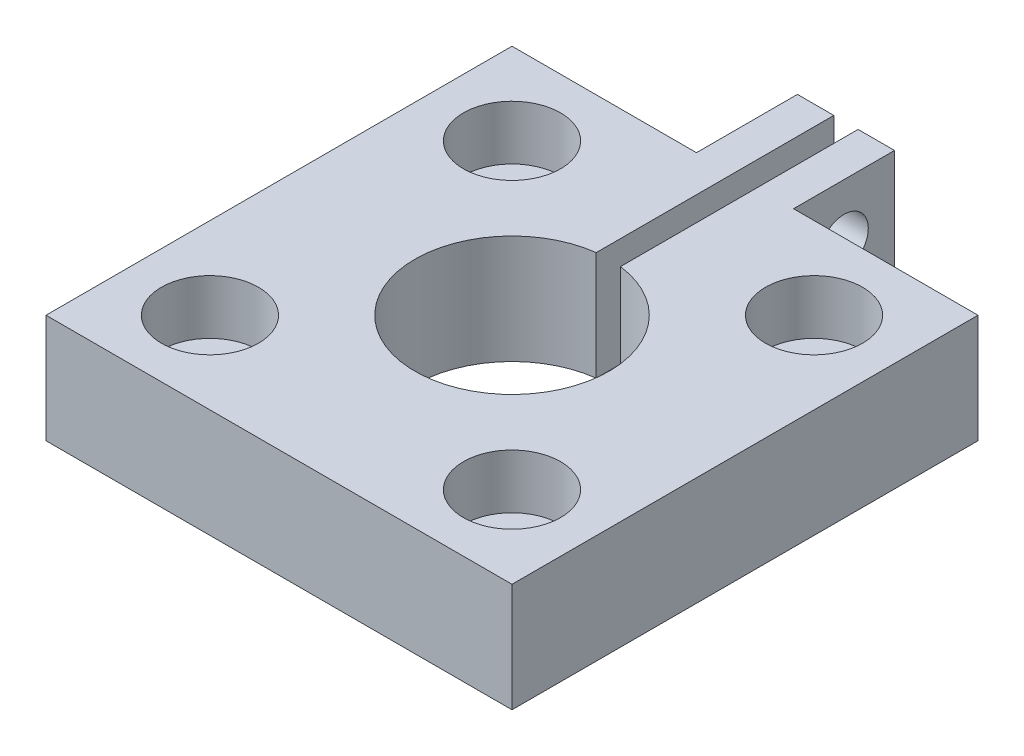
SolidWorks part; units mm, degrees
ref_plane "Front Plane" through (0, 0, 0) normal (0, 0, 1) x (1, 0, 0)
ref_plane "Top Plane" through (0, 0, 0) normal (0, 1, 0) x (1, 0, 0)
ref_plane "Right Plane" through (0, 0, 0) normal (1, 0, 0) x (0, 0, -1)
sketch "Sketch1" plane through (0, 0, 0) normal (0, 1, 0) x (1, 0, 0)
  line L0 (-0.3969, 10.922) -> (-0.3969, 7.62)
  line L1 (7.62, 7.62) -> (1.5875, 7.62)
  line L2 (7.62, 7.62) -> (7.62, -7.62)
  line L3 (7.62, -7.62) -> (-7.62, -7.62)
  line L4 (-7.62, 7.62) -> (-7.62, -7.62)
  line L5 (7.62, 7.62) -> (-7.62, -7.62) construction
  line L6 (7.62, -7.62) -> (-7.62, 7.62) construction
  line L7 (-0.3969, 7.62) -> (0.3969, 7.62)
  line L8 (-1.5875, 7.62) -> (-1.5875, 10.922)
  line L9 (-1.5875, 10.922) -> (-0.3969, 10.922)
  line L10 (1.5875, 7.62) -> (1.5875, 10.922)
  line L11 (0.3969, 10.922) -> (0.3969, 7.62)
  line L12 (-0.3969, 8.4053) -> (0.3969, 8.4053) construction
  line L13 (0.3969, 10.922) -> (1.5875, 10.922)
  line L14 (-1.5875, 10.132) -> (1.5875, 10.132) construction
  line L15 (-1.5875, 7.62) -> (-7.62, 7.62)
  line L16 (0.3969, 7.62) -> (-0.3969, 7.62)
  circle A0 centre (0, 0) radius 3.175
  point P0 (0, 0)
  point P19 (0, 8.4053)
  point P22 (0, 10.132)
  dimension "D1" = 6.35
  dimension "D2" = 15.24
  dimension "D3" = 3.175
  dimension "D4" = 3.302
  dimension "D5" = 0.7937
extrude "Boss-Extrude1" add sketch "Sketch1" along normal blind 3.556 contours L8 L15 L4 L3 L2 L1 L10 L13 L11 L7 L0 L9 A0
sketch "Sketch2" plane through (0, 3.556, 0) normal (0, 1, 0) x (1, 0, 0)
  line L0 (-4.9391, 4.9391) -> (4.9391, -4.9391) construction
  line L1 (4.9391, 4.9391) -> (-4.9391, -4.9391) construction
  line L2 (0, 0) -> (0, 1.9854) construction
  circle A0 centre (-4.9391, 4.9391) radius 0.7938
  circle A1 centre (4.9391, 4.9391) radius 0.7938
  circle A2 centre (4.9391, -4.9391) radius 0.7938
  circle A3 centre (-4.9391, -4.9391) radius 0.7937
  point P4 (0, 0)
  point P5 (0, 0)
  dimension "D2" = 1.5875
  dimension "D1" = 45
  dimension "D3" = 13.97
extrude "Cut-Extrude1" cut sketch "Sketch2" against normal through all
sketch "Sketch3" plane through (1.5875, 0, 0) normal (1, 0, 0) x (0, 0, -1)
  line L0 (7.62, 1.778) -> (10.922, 1.778) construction
  line L1 (7.62, 3.556) -> (7.62, 0) construction
  line L2 (10.922, 3.556) -> (10.922, 0) construction
  line L3 (9.271, 3.556) -> (9.271, 0) construction
  line L4 (7.62, 3.556) -> (10.922, 3.556) construction
  line L5 (7.62, 0) -> (10.922, 0) construction
  circle A0 centre (9.271, 1.778) radius 0.7937
  point P15 (9.271, 1.778)
  dimension "D1" = 1.5875
extrude "Cut-Extrude2" cut sketch "Sketch3" against normal blind 3.175
sketch "Sketch4" plane through (0, 3.556, 0) normal (0, 1, 0) x (1, 0, 0)
  line L0 (0.3969, 10.922) -> (0.3969, 7.62) construction
  line L1 (-0.3969, 7.62) -> (0.3969, 7.62)
  line L2 (-0.3969, 7.62) -> (-0.3969, 3.1501)
  line L3 (-0.3969, 3.1501) -> (0.3969, 3.1501)
  line L4 (0.3969, 7.62) -> (0.3969, 3.1501)
  circle A0 centre (0, 0) radius 3.175 construction
extrude "Cut-Extrude3" cut sketch "Sketch4" against normal through all
sketch "Sketch5" plane through (0, 3.556, 0) normal (0, 1, 0) x (1, 0, 0)
  circle A0 centre (-4.9391, 4.9391) radius 1.5875
  circle A1 centre (-4.9391, 4.9391) radius 0.7938 construction
  dimension "D1" = 3.175
extrude "Cut-Extrude4" cut sketch "Sketch5" against normal blind 1.778
mirror "Mirror1" about plane through (0, 0, 0) normal (0, 0, 1) of "Cut-Extrude4" second plane through (0, 0, 0) second plane normal (1, 0, 0)
